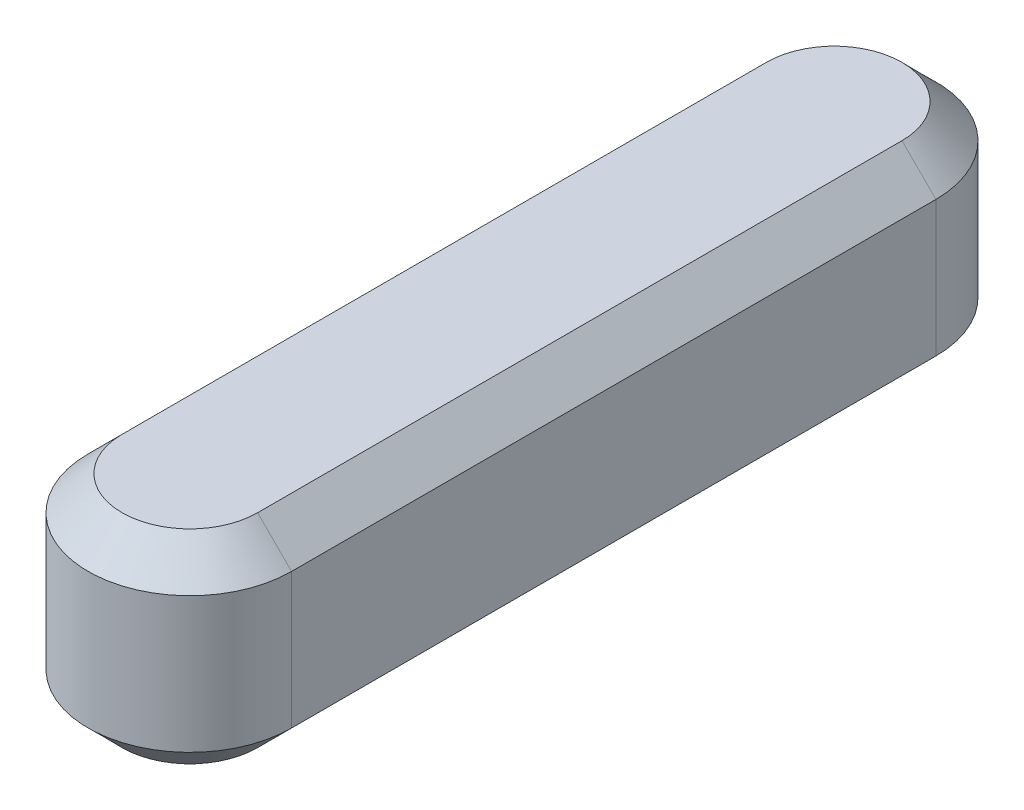
SolidWorks part; units mm, degrees
material "AISI 4340 Steel, normalized"
ref_plane "Front Plane" through (0, 0, 0) normal (0, 0, 1) x (1, 0, 0)
ref_plane "Top Plane" through (0, 0, 0) normal (0, 1, 0) x (1, 0, 0)
ref_plane "Right Plane" through (0, 0, 0) normal (1, 0, 0) x (0, 0, -1)
sketch "Sketch1" plane through (0, 0, 0) normal (0, 1, 0) x (1, 0, 0)
  line L0 (0, 0) -> (0, 19) construction
  line L1 (3, 0) -> (3, 19)
  line L2 (-3, 0) -> (-3, 19)
  arc A0 (3, 0) -> (-3, 0) centre (0, 0) cw
  arc A1 (3, 19) -> (-3, 19) centre (0, 19) ccw
  dimension "D1" = 19
  dimension "D2" = 3
  dimension "D3" = 3
extrude "Boss-Extrude1" add sketch "Sketch1" along normal blind 6
chamfer "Chamfer2" distance 1 angle 45 8 edges at (3, 6, -9.5) (0, 6, -22) (0, 6, 3) (-3, 6, -9.5) (-3, 0, -9.5) (0, 0, 3) (0, 0, -22) (3, 0, -9.5)
